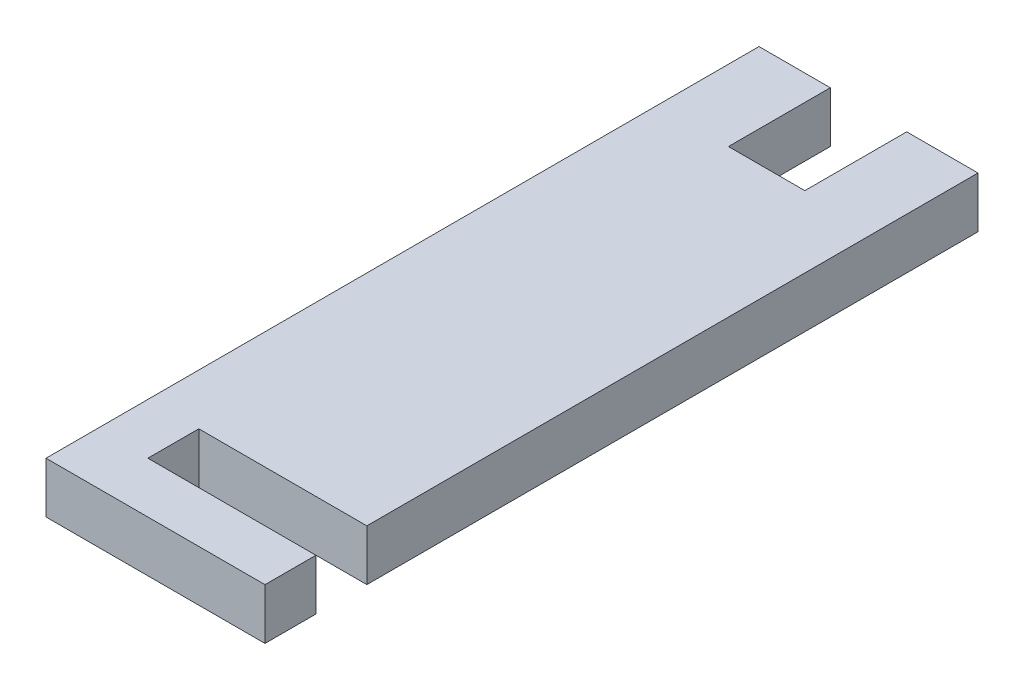
SolidWorks part; units mm, degrees
ref_plane "Front Plane" through (0, 0, 0) normal (0, 0, 1) x (1, 0, 0)
ref_plane "Top Plane" through (0, 0, 0) normal (0, 1, 0) x (1, 0, 0)
ref_plane "Right Plane" through (0, 0, 0) normal (1, 0, 0) x (0, 0, -1)
sketch "Sketch1" plane through (0, 0, 0) normal (0, 1, 0) x (1, 0, 0)
  line L0 (10.75, -25) -> (10.75, -30) construction
  line L1 (-10.75, 35) -> (-3.75, 35)
  line L2 (-10.75, 35) -> (-10.75, -35)
  line L3 (-10.75, -35) -> (10.75, -35)
  line L4 (10.75, 35) -> (10.75, -25)
  line L5 (-10.75, 35) -> (10.75, -35) construction
  line L6 (-10.75, -35) -> (10.75, 35) construction
  line L7 (10.75, -30) -> (-5.75, -30)
  line L8 (10.75, -30) -> (10.75, -25) construction
  line L9 (10.75, -25) -> (-5.75, -25)
  line L10 (-5.75, -30) -> (-5.75, -25)
  line L11 (10.75, -30) -> (10.75, -35)
  line L12 (-3.75, 35) -> (3.75, 35) construction
  line L13 (-3.75, 25) -> (3.75, 25)
  line L14 (-3.75, 25) -> (-3.75, 35)
  line L15 (-3.75, 35) -> (3.75, 35) construction
  line L16 (3.75, 25) -> (3.75, 35)
  line L17 (-3.75, 25) -> (3.75, 35) construction
  line L18 (-3.75, 35) -> (3.75, 25) construction
  line L19 (3.75, 35) -> (10.75, 35)
  point P0 (0, 0)
  point P10 (0, 30)
  point P15 (0, 0)
  dimension "D1" = 70
  dimension "D2" = 21.5
  dimension "D3" = 5
  dimension "D4" = 5
  dimension "D5" = 5
  dimension "D6" = 7.5
  dimension "D7" = 10
extrude "Boss-Extrude1" add sketch "Sketch1" along normal blind 5
